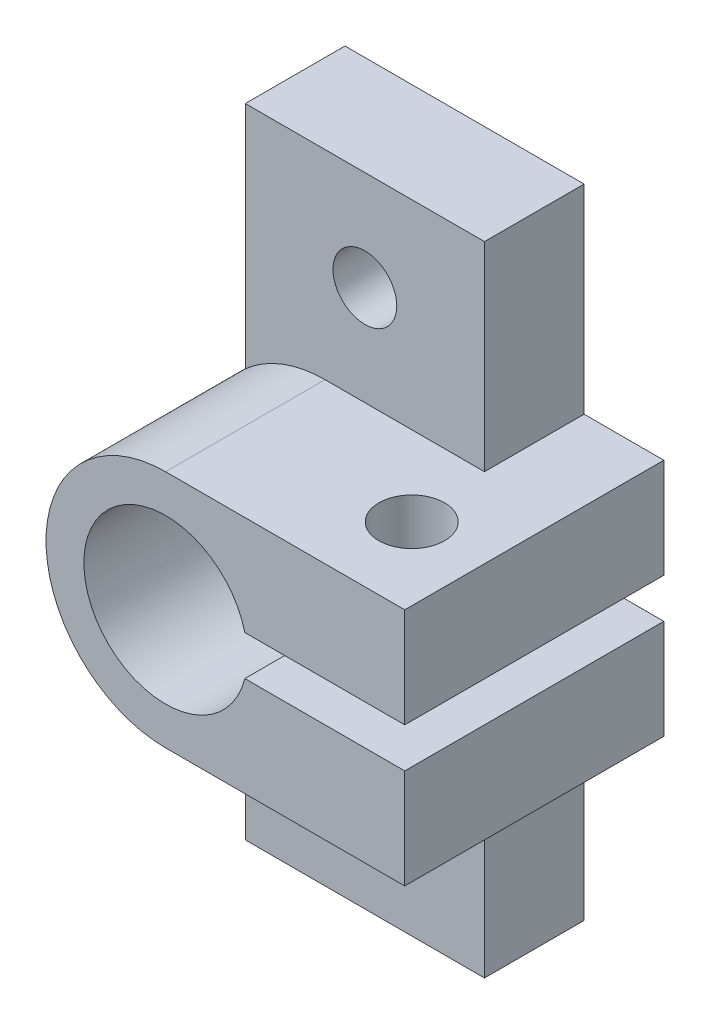
SolidWorks part; units mm, degrees
ref_plane "Plano frontal" through (0, 0, 0) normal (0, 0, 1) x (1, 0, 0)
ref_plane "Plano superior" through (0, 0, 0) normal (0, 1, 0) x (1, 0, 0)
ref_plane "Plano direito" through (0, 0, 0) normal (1, 0, 0) x (0, 0, -1)
sketch "Esboço1" plane through (0, 0, 0) normal (0, 0, 1) x (1, 0, 0)
  line L0 (-4, 16) -> (-4, 0.9)
  line L1 (8, -16) -> (8, -1)
  line L2 (0, 0) -> (8, 0) construction
  line L3 (3.9762, -1) -> (8, -1)
  line L4 (3.9762, 1) -> (8, 1)
  line L5 (0, 1) -> (8, 1) construction
  line L6 (0, -1) -> (8, -1) construction
  line L7 (8, 1) -> (8, 16)
  line L8 (-4, 16) -> (8, 16)
  line L9 (8, -16) -> (-4, -16)
  line L10 (-4, -0.9) -> (-4, -16)
  arc A0 (3.9762, 1) -> (-4, 0.9) centre (0, 0) ccw
  circle A1 centre (2, 11) radius 1.6
  circle A2 centre (2, -11) radius 1.6
  arc A3 (-4, -0.9) -> (3.9762, -1) centre (0, 0) ccw
  point P7 (2, 16)
  dimension "D1" = 12
  dimension "D2" = 3.2
  dimension "D3" = 8.2
  dimension "D4" = 32
  dimension "D7" = 22
  dimension "D8" = 4
  dimension "D5" = 1
  dimension "D6" = 1
extrude "Ressalto-extrusão1" add sketch "Esboço1" along normal blind 5 contours A3 L10 L9 L1 L3 A2 | A0 L4 L7 L8 L0 A1
sketch "Esboço2" plane through (0, 0, 5) normal (0, 0, 1) x (1, 0, 0)
  line L0 (12, 6) -> (12, 1)
  line L2 (12, 6) -> (0, 6)
  line L3 (12, -1) -> (12, -6)
  line L10 (12, -6) -> (0, -6)
  line L11 (0, 0) -> (11.2942, 0) construction
  line L12 (12, -1) -> (3.9762, -1)
  line L13 (3.9762, 1) -> (12, 1)
  arc A0 (0, -6) -> (0, 6) centre (0, 0) cw
  arc A1 (3.9762, 1) -> (-4, 0.9) centre (0, 0) ccw construction
  arc A8 (3.9762, 1) -> (3.9762, -1) centre (0, 0) ccw
  dimension "D2" = 6
  dimension "D3" = 12
  dimension "D4" = 2
extrude "Ressalto-extrusão2" add sketch "Esboço2" along normal blind 8 and the other way through all
sketch "Esboço3" plane through (0, 6, 0) normal (0, -1, 0) x (1, 0, 0)
  line L0 (5.95, 13) -> (5.95, 5) construction
  line L1 (12, 0) -> (12, 13) construction
  line L2 (-6, 5) -> (12, 5) construction
  line L3 (12, 0) -> (12, 13) construction
  line L5 (-6, 13) -> (-6, 0) construction
  line L6 (-4, 5) -> (8, 5) construction
  line L7 (12, 13) -> (0, 13) construction
  circle A0 centre (8.35, 9) radius 1.65
  point P13 (5.95, 9)
  dimension "D1" = 3.3
  dimension "D3" = 2
  dimension "D2" = 2.4
extrude "Corte-extrusão1" cut sketch "Esboço3" against normal through all both and the other way through all
sketch "Esboço4" plane through (0, 0, 0) normal (0, 0, -1) x (-1, 0, 0)
  line L0 (4, 16) -> (26, 16)
  line L1 (26, 16) -> (26, 13)
  line L2 (26, 13) -> (4, 13)
  line L3 (4, 16) -> (4, 4.4721) construction
  line L4 (4, 4.4721) -> (4, 13)
  line L5 (4.1, 1.5) -> (26, 1.5)
  line L6 (26, 1.5) -> (26, -1.5)
  line L7 (26, 0) -> (4.1, 0) construction
  line L8 (4.1, 1.5) -> (4.1, -1.5)
  line L9 (4, -16) -> (0, -6)
  line L10 (4.1, -1.5) -> (26, -1.5)
  line L11 (4, -4.4721) -> (4, -13)
  line L12 (26, -13) -> (4, -13)
  line L13 (26, -16) -> (26, -13)
  line L14 (4, 16) -> (0, 6)
  line L15 (4, -16) -> (26, -16)
  arc A0 (-3.9762, -1) -> (-3.9762, 1) centre (0, 0) ccw construction
  arc A2 (4, 4.4721) -> (0, 6) centre (0, 0) ccw construction
  arc A3 (4, 4.4721) -> (0, 6) centre (0, 0) ccw
  arc A4 (4, -4.4721) -> (0, -6) centre (0, 0) cw
  dimension "D1" = 22
  dimension "D2" = 3
  dimension "D3" = 1.5
extrude "Ressalto-extrusão3" [suppressed] add sketch "Esboço4" against normal blind 12
sketch "Esboço5" [suppressed] plane through (0, -15, 0) normal (0, -1, 0) x (1, 0, 0)
  line L0 (-26, 12) -> (-26, 0) construction
  line L1 (8, 5) -> (8, 0) construction
  line L2 (8, 0) -> (-26, 0) construction
  line L3 (-19, 12) -> (-26, 12)
  line L5 (-19, 0) -> (-26, 0)
  line L6 (-26, 12) -> (-26, 0)
  circle A0 centre (-19, 6) radius 1.6
  arc A1 (-19, 12) -> (-19, 0) centre (-19, 6) ccw
  point P5 (-26, 6)
  dimension "D2" = 3.2
  dimension "D1" = 27
extrude "Corte-extrusão2" [suppressed] cut sketch "Esboço5" against normal through all
fillet "Filete1" [suppressed] radius 4
